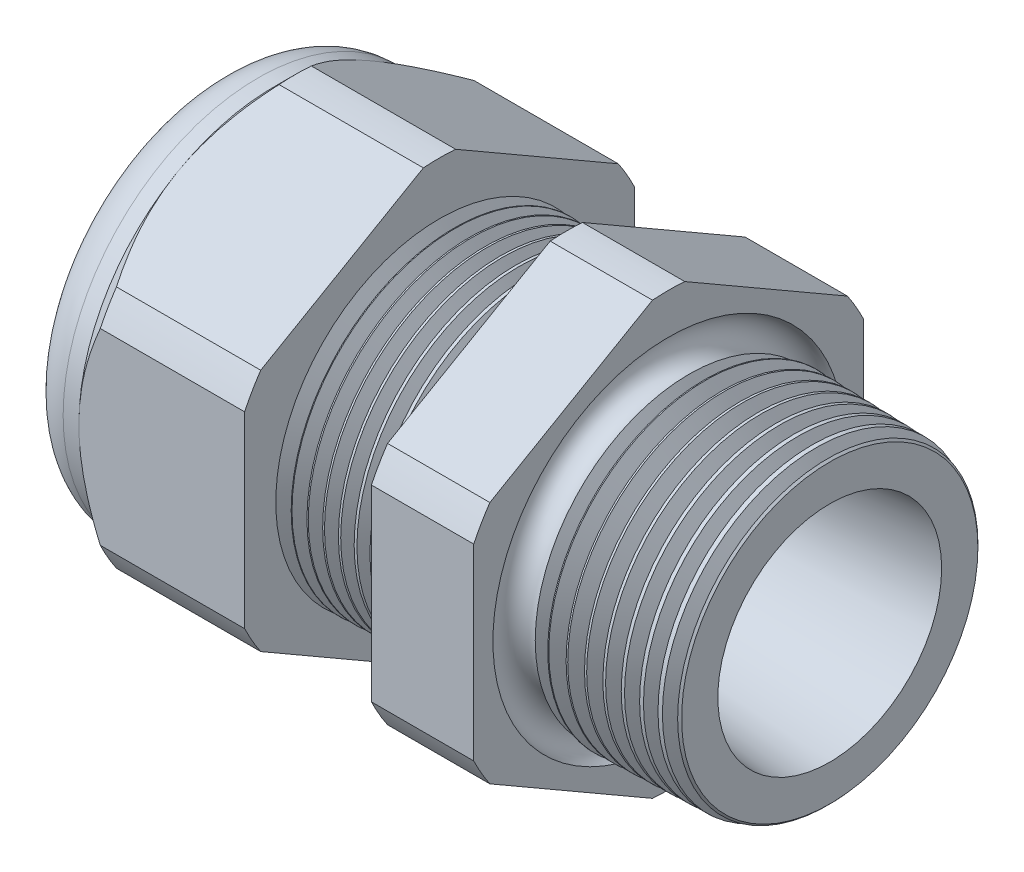
SolidWorks part; units mm, degrees
ref_plane "Front Plane" through (0, 0, 0) normal (0, 0, 1) x (1, 0, 0)
ref_plane "Top Plane" through (0, 0, 0) normal (0, 1, 0) x (1, 0, 0)
ref_plane "Right Plane" through (0, 0, 0) normal (1, 0, 0) x (0, 0, -1)
sketch "Sketch10" plane through (0, 0, 0) normal (0, 0, 1) x (1, 0, 0)
  line L0 (0, 0) -> (-115.3565, 0) construction
  line L1 (-29.972, 3.937) -> (-19.072, 3.937)
  line L2 (0, 5.4696) -> (0, 7.5016)
  line L3 (-7.874, 7.7078) -> (0, 7.5016)
  line L4 (-7.874, 19.05) -> (-7.874, 7.7078)
  line L5 (-7.874, 19.05) -> (-12.874, 19.05)
  line L6 (-12.874, 19.05) -> (-12.874, 7.8387)
  line L7 (-19.072, 8.001) -> (-12.874, 7.8387)
  line L8 (-19.072, 8.001) -> (-19.072, 19.05)
  line L9 (-19.072, 19.05) -> (-27.172, 19.05)
  line L10 (-27.172, 19.05) -> (-27.172, 9.525)
  line L11 (-27.172, 9.525) -> (-29.972, 9.525)
  line L12 (-29.972, 9.525) -> (-29.972, 3.937)
  line L13 (-19.072, 3.937) -> (0, 5.4696)
  dimension "D1" = 29.972
  dimension "D2" = 7.874
  dimension "D3" = 1.5
  dimension "D4" = 2.032
  dimension "A" = 16.002
  dimension "D6" = 19.05
  dimension "D8" = 38.1
  dimension "D9" = 2.8
  dimension "D10" = 8.1
  dimension "D11" = 5
  dimension "D" = 7.874
revolve "Revolve2" add sketch "Sketch10" angle 360 about L0
sketch "Sketch12" plane through (-27.172, 0, 0) normal (-1, 0, 0) x (0, 0, 1)
  line L1 (-0.7885, 10.5433) -> (-8.7365, 5.9545)
  line L2 (-9.525, 4.5888) -> (-9.525, -4.5888)
  line L3 (-8.7365, -5.9545) -> (-0.7885, -10.5433)
  line L4 (0.7885, -10.5433) -> (8.7365, -5.9545)
  line L5 (9.525, -4.5888) -> (9.525, 4.5888)
  line L6 (8.7365, 5.9545) -> (0.7885, 10.5433)
  circle A0 centre (0, 0) radius 9.525 construction
  arc A1 (0.7885, 10.5433) -> (-0.7885, 10.5433) centre (0, 0) ccw
  arc A2 (-8.7365, 5.9545) -> (-9.525, 4.5888) centre (0, 0) ccw
  arc A3 (-9.525, -4.5888) -> (-8.7365, -5.9545) centre (0, 0) ccw
  arc A4 (-0.7885, -10.5433) -> (0.7885, -10.5433) centre (0, 0) ccw
  arc A5 (8.7365, -5.9545) -> (9.525, -4.5888) centre (0, 0) ccw
  arc A6 (9.525, 4.5888) -> (8.7365, 5.9545) centre (0, 0) ccw
  dimension "D2" = 21.1455
  dimension "D1" = 19.05
extrude "Cut-Extrude2" cut sketch "Sketch12" against normal through all flip side to cut
fillet "Fillet4" radius 2.032 1 edges at (-29.972, 0, -9.525)
sketch "Sketch19" plane through (-27.172, 0, 0) normal (-1, 0, 0) x (0, 0, 1)
  line L0 (9.525, 0) -> (9.525, 4.5888) construction
  circle A0 centre (0, 0) radius 9.525
extrude "Cut-Extrude3" cut sketch "Sketch19" against normal blind 2 draft 45 flip side to cut
chamfer "Chamfer1" distance 0.254 angle 45 1 edges at (0, 0, -7.5016)
sketch "Sketch21" plane through (-29.972, 0, 0) normal (-1, 0, 0) x (0, 0, 1)
  circle A0 centre (0, 0) radius 3.937
  circle A2 centre (0, 0) radius 3.937 construction
extrude "plug" add sketch "Sketch21" against normal blind 3.81 separate body
sketch "Sketch22" plane through (-29.972, 0, 0) normal (-1, 0, 0) x (0, 0, 1)
  circle A0 centre (0, 0) radius 3.683
  circle A1 centre (0, 0) radius 3.937 construction
  dimension "D1" = 0.254
extrude "Cut-Extrude4" cut sketch "Sketch22" against normal blind 0.508
sketch "Sketch27" plane through (-29.464, 0, 0) normal (-1, 0, 0) x (0, 0, 1)
  line L0 (-4.3624, 0) -> (4.3624, 0) construction
  circle A0 centre (-2.7904, 0) radius 0.889
  circle A1 centre (0, 0) radius 3.683 construction
  dimension "D1" = 0.0036
  dimension "holedia" = 1.778
extrude "plugholes" cut sketch "Sketch27" against normal through all
pattern_circular "CirPattern1" count 4 over 360 about axis through (0, 0, 0) along (1, 0, 0) of "plugholes"
sketch "Sketch28" [suppressed] plane through (-29.464, 0, 0) normal (-1, 0, 0) x (0, 0, 1)
  circle A0 centre (0, 0) radius 0.762
  dimension "midholedia" = 1.778
extrude "midhole" [suppressed] cut sketch "Sketch28" against normal through all
sketch "Sketch29" plane through (0, 0, 0) normal (0, 0, 1) x (1, 0, 0)
  line L0 (-19.072, 8.001) -> (-18.339, 7.9818)
  line L1 (-12.874, 7.8387) -> (-19.072, 8.001) construction
  line L2 (-18.339, 7.9818) -> (-18.7221, 7.3566)
  line L3 (-18.7221, 7.3566) -> (-19.072, 8.001)
  dimension "D1" = 60
  dimension "D2" = 60
  dimension "D3" = 0.635
revolve "Cut-Revolve1" cut sketch "Sketch29" angle 360 about axis through (0, 0, 0) along (-1, 0, 0)
pattern_linear "LPattern1" count 8 spacing 0.762 along (1, 0, 0) of "Cut-Revolve1"
sketch "Sketch30" plane through (0, 0, 0) normal (0, 0, 1) x (1, 0, 0)
  line L0 (-7.874, 7.7078) -> (-6.9944, 7.6847)
  line L1 (-7.874, 10.5433) -> (-7.874, 5.9545) construction
  line L2 (-0.2539, 7.5082) -> (-7.874, 7.7078) construction
  line L3 (-6.9944, 7.6847) -> (-7.4542, 6.9345)
  line L4 (-7.4542, 6.9345) -> (-7.874, 7.7078)
  dimension "D1" = 60
  dimension "D2" = 60
  dimension "D3" = 0.762
revolve "Cut-Revolve2" cut sketch "Sketch30" angle 360 about axis through (0, 0, 0) along (-1, 0, 0)
pattern_linear "LPattern2" count 9 spacing 0.889 along (1, 0, 0) of "Cut-Revolve2"
sketch "Sketch31" [suppressed] plane through (-38.354, 0, 0) normal (-1, 0, 0) x (0, 0, 1)
  line L0 (-1.905, 1.905) -> (1.905, 1.905)
  line L1 (-1.905, -1.905) -> (1.905, -1.905)
  circle A0 centre (0, 0) radius 1.905 construction
  arc A1 (-1.905, 1.905) -> (-1.905, -1.905) centre (-1.905, 0) ccw
  arc A2 (1.905, 1.905) -> (1.905, -1.905) centre (1.905, 0) cw
extrude "Cut-Extrude5" [suppressed] cut sketch "Sketch31" against normal through all
sketch "Sketch32" plane through (0, 0, 0) normal (0, 0, 1) x (1, 0, 0)
  line L0 (-7.874, 10.5433) -> (-7.874, 5.9545) construction
  circle A0 centre (-7.747, 7.7078) radius 0.889
  dimension "D2" = 1.778
  dimension "D1" = 0.127
revolve "Cut-Revolve3" cut sketch "Sketch32" angle 360 about axis through (0, 0, 0) along (-1, 0, 0)
